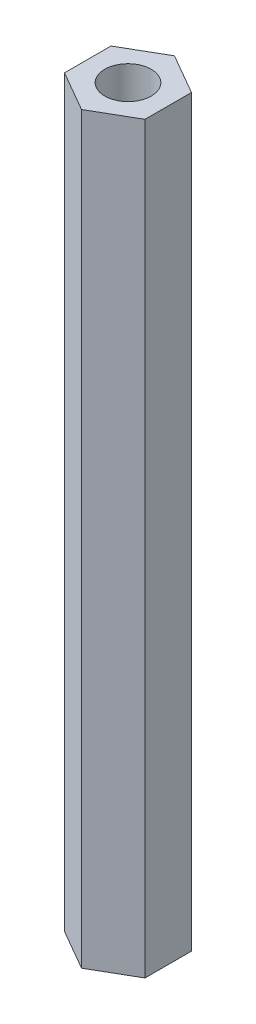
SolidWorks part; units mm, degrees
ref_plane "Face" through (0, 0, 0) normal (0, 0, 1) x (1, 0, 0)
ref_plane "Dessus" through (0, 0, 0) normal (0, 1, 0) x (1, 0, 0)
ref_plane "Droite" through (0, 0, 0) normal (1, 0, 0) x (0, 0, -1)
sketch "Esquisse1" plane through (0, 0, 0) normal (0, 1, 0) x (1, 0, 0)
  line L0 (0, 0) -> (0, 5.5688) construction
  line L1 (0, 5) -> (-4.3301, 2.5)
  line L2 (-4.3301, 2.5) -> (-4.3301, -2.5)
  line L3 (-4.3301, -2.5) -> (0, -5)
  line L4 (0, -5) -> (4.3301, -2.5)
  line L5 (4.3301, -2.5) -> (4.3301, 2.5)
  line L6 (4.3301, 2.5) -> (0, 5)
  circle A0 centre (0, 0) radius 4.3301 construction
  circle A1 centre (0, 0) radius 2.5
  dimension "D1" = 10
  dimension "D2" = 5
extrude "Extrusion1" add sketch "Esquisse1" along normal blind 80
